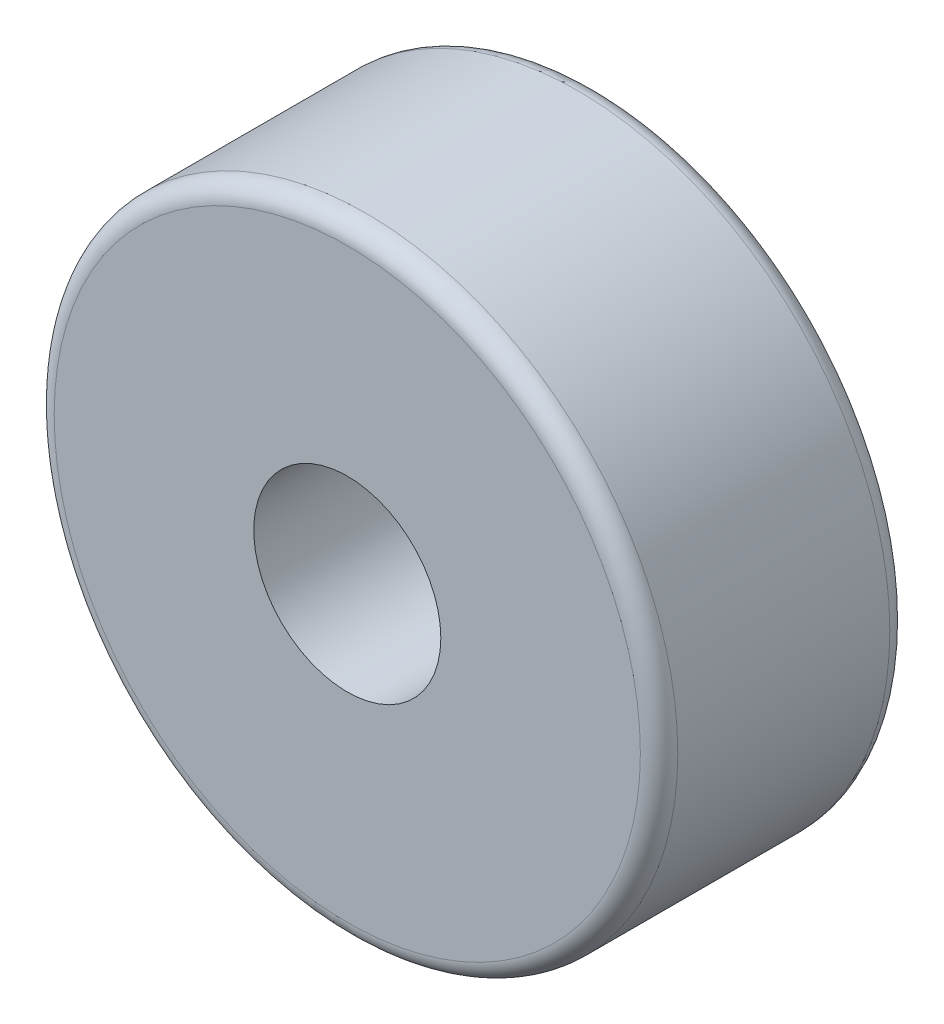
SolidWorks part; units mm, degrees
ref_plane "Front Plane" through (0, 0, 0) normal (0, 0, 1) x (1, 0, 0)
ref_plane "Top Plane" through (0, 0, 0) normal (0, 1, 0) x (1, 0, 0)
ref_plane "Right Plane" through (0, 0, 0) normal (1, 0, 0) x (0, 0, -1)
sketch "Sketch1" plane through (0, 0, 0) normal (0, 0, 1) x (1, 0, 0)
  circle A0 centre (0, 0) radius 5
  circle A1 centre (0, 0) radius 1.5
  dimension "D1" = 3
  dimension "D2" = 10
extrude "Boss-Extrude1" add sketch "Sketch1" along normal blind 4
fillet "Fillet1" radius 0.3 2 edges at (5, 0, 0) (5, 0, 4)
